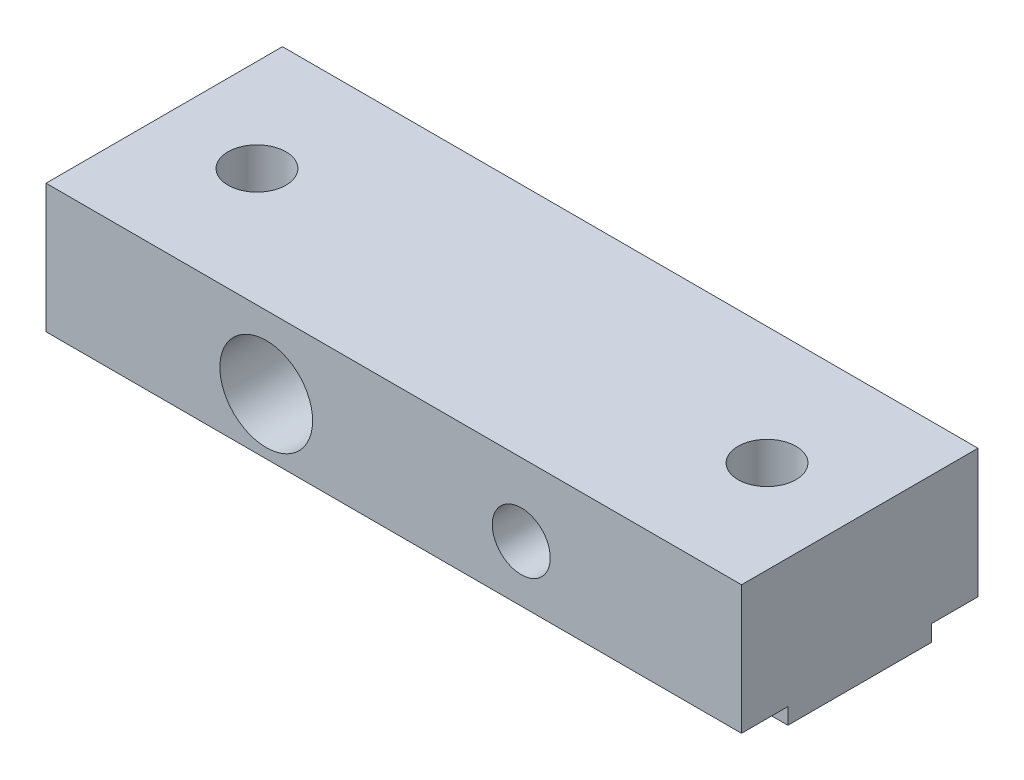
SolidWorks part; units mm, degrees
ref_plane "Front Plane" through (0, 0, 0) normal (0, 0, 1) x (1, 0, 0)
ref_plane "Top Plane" through (0, 0, 0) normal (0, 1, 0) x (1, 0, 0)
ref_plane "Right Plane" through (0, 0, 0) normal (1, 0, 0) x (0, 0, -1)
sketch "Sketch1" plane through (0, 0, 0) normal (0, 1, 0) x (1, 0, 0)
  line L1 (0, 0) -> (30, 0)
  line L2 (0, 0) -> (0, 10.2)
  line L3 (0, 10.2) -> (30, 10.2)
  line L4 (30, 0) -> (30, 10.2)
  dimension "D1" = 30
  dimension "D2" = 10.2
extrude "Boss-Extrude1" add sketch "Sketch1" along normal blind 6.25
hole_wizard "Ø4.0 (4) Diameter Hole1" positions "Sketch3" profile "Sketch2" hole size "Ø4.0" standard "Ansi Metric" end condition through all
sketch "Sketch3" plane through (0, 0, 0) normal (0, 0, 1) x (1, 0, 0)
  line L0 (0, 3.125) -> (9.5, 3.125) construction
  line L2 (9.5, 3.125) -> (20.5, 3.125) construction
  line L7 (0, 6.25) -> (0, 0) construction
  line L8 (0, 0) -> (30, 0) construction
  line L9 (20.5, 3.125) -> (30, 3.125) construction
  line L13 (30, 6.25) -> (30, 0) construction
  point P0 (9.5, 3.125)
  dimension "D2" = 11
sketch "Sketch2" plane through (9.5, 3.125, 0) normal (1, 0, 0) x (0, -1, 0)
  line L0 (0, 0) -> (0, 10.2)
  line L1 (0, 10.2) -> (2, 10.2)
  line L2 (2, 10.2) -> (2, 0)
  line L5 (2, 0) -> (0, 0)
  line L11 (0, -6.35) -> (0, 107.95) construction
  dimension "Thru Hole Dia." = 4
  dimension "Thru Hole Depth" = 10.2
ref_point "Point2"
hole_wizard "Ø2.5 (2.5) Diameter Hole2" positions "Sketch8" profile "Sketch7" hole size "Ø2.5" standard "Ansi Metric" end condition through all
sketch "Sketch8" plane through (0, 0, 0) normal (0, 0, 1) x (1, 0, 0)
  point P0 (20.5, 3.125)
sketch "Sketch7" plane through (20.5, 3.125, 0) normal (1, 0, 0) x (0, -1, 0)
  line L0 (0, 0) -> (0, 10.2)
  line L1 (0, 10.2) -> (1.25, 10.2)
  line L2 (1.25, 10.2) -> (1.25, 0)
  line L5 (1.25, 0) -> (0, 0)
  line L11 (0, -6.35) -> (0, 107.95) construction
  dimension "Thru Hole Dia." = 2.5
  dimension "Thru Hole Depth" = 10.2
hole_wizard "Ø2.5 (2.5) Diameter Hole1" positions "Sketch5" profile "Sketch4" hole size "Ø2.5" standard "Ansi Metric" end condition through all
sketch "Sketch5" plane through (0, 6.25, 0) normal (0, 1, 0) x (-1, 0, 0)
  line L3 (-26, -5.1) -> (-30, -5.1) construction
  line L5 (-30, 0) -> (-30, -10.2) construction
  line L6 (0, -5.1) -> (-4, -5.1) construction
  line L7 (0, -10.2) -> (0, 0) construction
  line L8 (-4, -5.1) -> (-26, -5.1) construction
  point P0 (-4, -5.1)
  point P1 (-26, -5.1)
  dimension "D1" = 4
sketch "Sketch4" plane through (4, 6.25, -5.1) normal (1, 0, 0) x (0, 0, 1)
  line L0 (0, 0) -> (0, 6.25)
  line L1 (0, 6.25) -> (1.25, 6.25)
  line L2 (1.25, 6.25) -> (1.25, 0)
  line L5 (1.25, 0) -> (0, 0)
  line L11 (0, -6.35) -> (0, 107.95) construction
  dimension "Thru Hole Dia." = 2.5
  dimension "Thru Hole Depth" = 6.25
sketch "Sketch6" plane through (30, 0, 0) normal (1, 0, 0) x (0, 0, -1)
  line L1 (10.2, 0) -> (8.2, 0)
  line L2 (10.2, 0) -> (10.2, 0.7)
  line L3 (10.2, 0.7) -> (8.2, 0.7)
  line L4 (8.2, 0) -> (8.2, 0.7)
  dimension "D1" = 0.7
  dimension "D2" = 2
extrude "Cut-Extrude1" cut sketch "Sketch6" against normal through all
ref_plane "Plane1" through (0, 0, -5.1) normal (0, 0, 1) x (1, 0, 0)
mirror "Mirror1" about plane through (0, 0, -5.1) normal (0, 0, 1) of "Cut-Extrude1"
